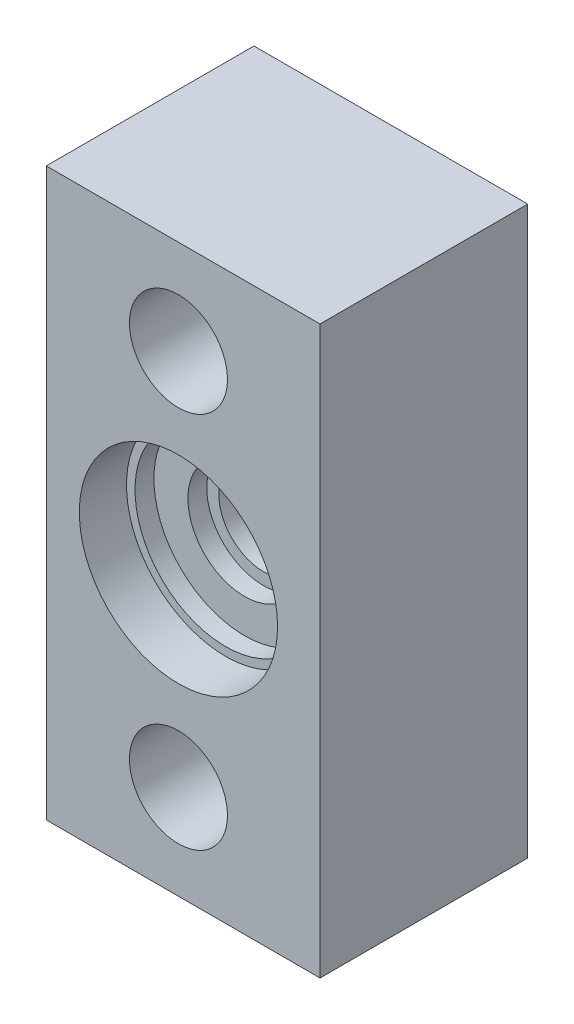
SolidWorks part; units mm, degrees
material "6061-T4 (SS)"
ref_plane "Front Plane" through (0, 0, 0) normal (0, 0, 1) x (1, 0, 0)
ref_plane "Top Plane" through (0, 0, 0) normal (0, 1, 0) x (1, 0, 0)
ref_plane "Right Plane" through (0, 0, 0) normal (1, 0, 0) x (0, 0, -1)
sketch "Sketch1" plane through (0, 0, 0) normal (0, 0, 1) x (1, 0, 0)
  line L5 (-6, 6) -> (0, 0) construction
  line L6 (0, 0) -> (6, 6) construction
  line L7 (7.5, 15) -> (-7.5, 15)
  line L8 (7.5, 15) -> (7.5, -15)
  line L9 (7.5, -15) -> (-7.5, -15)
  line L10 (-7.5, 15) -> (-7.5, -15)
  line L11 (7.5, 15) -> (-7.5, -15) construction
  line L12 (7.5, -15) -> (-7.5, 15) construction
  point P0 (0, 0)
  dimension "D1" = 15
  dimension "D4" = 30
extrude "Boss-Extrude1" add sketch "Sketch1" along normal blind 6
sketch "Sketch2" plane through (0, 0, 6) normal (0, 0, 1) x (1, 0, 0)
  circle A0 centre (0, 0) radius 5.25
  dimension "D1" = 10.5
extrude "Cut-Extrude1" cut sketch "Sketch2" against normal blind 2.5 contours A0
sketch "Sketch4" plane through (0, 0, 3.5) normal (0, 0, 1) x (1, 0, 0)
  circle A0 centre (0, 0) radius 4.8
  dimension "D1" = 9.6
extrude "Cut-Extrude3" cut sketch "Sketch4" against normal blind 1
sketch "Sketch5" plane through (0, 0, 2.5) normal (0, 0, 1) x (1, 0, 0)
  circle A0 centre (0, 0) radius 2.36
  dimension "D1" = 4.72
extrude "Cut-Extrude4" cut sketch "Sketch5" against normal blind 5 and the other way through all
sketch "Sketch6" plane through (0, 0, 0) normal (0, 0, 1) x (1, 0, 0)
  line L0 (-7, 15) -> (-7, -15)
  line L3 (7.5, 15) -> (-7.5, 15) construction
  line L4 (-7.5, -15) -> (7.5, -15) construction
  circle A0 centre (0, 0) radius 5.25 construction
  point P6 (-7, 0)
  dimension "D1" = 7
extrude "Cut-Extrude6" cut sketch "Sketch6" against normal through all and the other way through all flip side to cut
sketch "Sketch11" plane through (0, 0, 0) normal (0, 0, -1) x (-1, 0, 0)
  line L1 (7, 15) -> (-7.5, 15)
  line L2 (7, 15) -> (7, -15)
  line L3 (7, -15) -> (-7.5, -15)
  line L4 (-7.5, 15) -> (-7.5, -15)
extrude "Boss-Extrude5" add sketch "Sketch11" along normal blind 5
sketch "Sketch12" plane through (0, 0, -5) normal (0, 0, -1) x (-1, 0, 0)
  circle A0 centre (0, 0) radius 4
  dimension "D1" = 8
extrude "Cut-Extrude8" cut sketch "Sketch12" against normal blind 5
sketch "Sketch13" plane through (0, 0, -5) normal (0, 0, -1) x (-1, 0, 0)
  line L2 (7, 15) -> (-7.5, 15) construction
  line L3 (0, 15) -> (0, -15) construction
  line L4 (-7.5, -15) -> (7, -15) construction
  circle A1 centre (0, -10) radius 2.595
  circle A2 centre (0, 10) radius 2.595
  point P0 (0, 5)
  point P4 (0, -5)
  dimension "D3" = 5.19
  dimension "D4" = 5.19
  dimension "D1" = 5
  dimension "D2" = 5
extrude "Cut-Extrude9" cut sketch "Sketch13" against normal through all
sketch "Sketch14" plane through (0, 0, 2.5) normal (0, 0, 1) x (1, 0, 0)
  circle A0 centre (0, 0) radius 3
  dimension "D1" = 6
extrude "Cut-Extrude10" cut sketch "Sketch14" against normal blind 1
